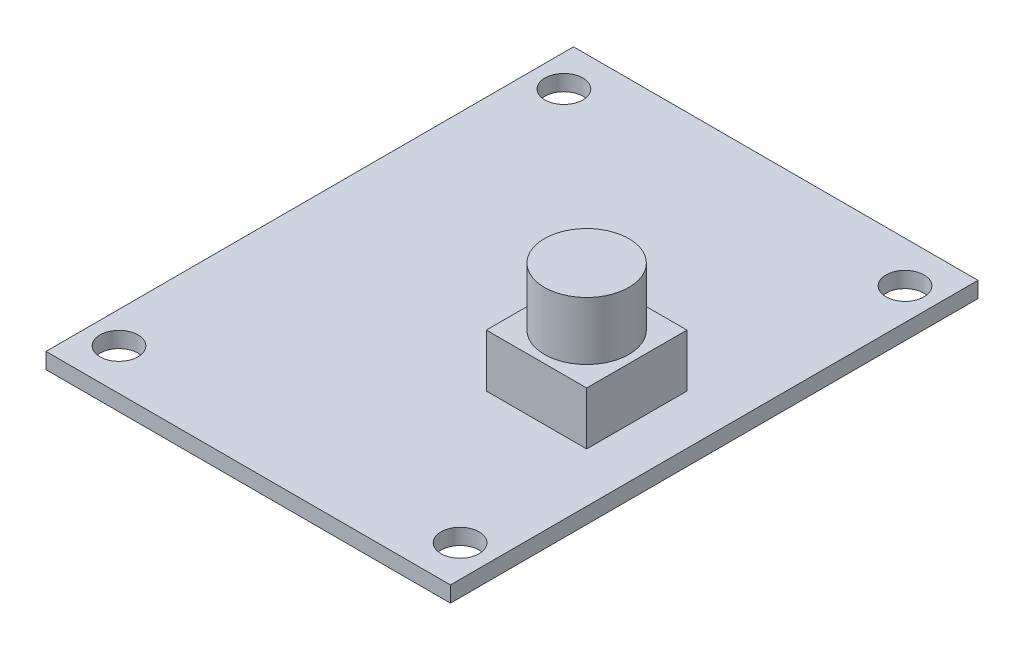
SolidWorks part; units mm, degrees
ref_plane "Front Plane" through (0, 0, 0) normal (0, 0, 1) x (1, 0, 0)
ref_plane "Top Plane" through (0, 0, 0) normal (0, 1, 0) x (1, 0, 0)
ref_plane "Right Plane" through (0, 0, 0) normal (1, 0, 0) x (0, 0, -1)
sketch "Sketch1" plane through (0, 0, 0) normal (0, 1, 0) x (1, 0, 0)
  line L1 (19.15, 24.98) -> (-19.15, 24.98)
  line L2 (19.15, 24.98) -> (19.15, -24.98)
  line L3 (19.15, -24.98) -> (-19.15, -24.98)
  line L4 (-19.15, 24.98) -> (-19.15, -24.98)
  line L5 (19.15, 24.98) -> (-19.15, -24.98) construction
  line L6 (19.15, -24.98) -> (-19.15, 24.98) construction
  circle A0 centre (-16.15, 21.0667) radius 1.8
  circle A1 centre (16.15, 21.0667) radius 1.8
  circle A2 centre (-16.15, -21.0667) radius 1.8
  circle A3 centre (16.15, -21.0667) radius 1.8
  point P0 (0, 0)
  point P14 (0, 0)
  point P15 (0, 0)
  point P16 (26.6052, -40.2079)
  point P17 (0, 0)
  dimension "D1" = 3.6
  dimension "D2" = 49.96
  dimension "D3" = 3
  dimension "D4" = 38.3
extrude "Boss-Extrude1" add sketch "Sketch1" along normal blind 1.5 contours A2 | A3 | L4 L3 L2 L1 | A0 | A1
sketch "Sketch3" plane through (0, 1.5, 0) normal (0, 1, 0) x (1, 0, 0)
  line L0 (19.15, -24.98) -> (-19.15, -24.98) construction
  line L1 (4.95, 2.12) -> (14.45, 2.12)
  line L2 (4.95, 2.12) -> (4.95, -7.38)
  line L3 (4.95, -7.38) -> (14.45, -7.38)
  line L4 (14.45, 2.12) -> (14.45, -7.38)
  line L5 (19.15, 24.98) -> (19.15, -24.98) construction
  dimension "D1" = 9.5
  dimension "D2" = 9.5
  dimension "D3" = 27.1
  dimension "D4" = 4.7
extrude "Boss-Extrude2" add sketch "Sketch3" along normal blind 5 separate body
sketch "Sketch5" plane through (0, 6.5, 0) normal (0, 1, 0) x (1, 0, 0)
  line L0 (4.95, 2.12) -> (14.45, -7.38)
  line L1 (4.95, -7.38) -> (14.45, 2.12)
  circle A0 centre (9.7, -2.63) radius 4
  point P8 (9.7, -2.63)
  dimension "D1" = 8
extrude "Boss-Extrude3" add sketch "Sketch5" along normal blind 5.5 contours A0
